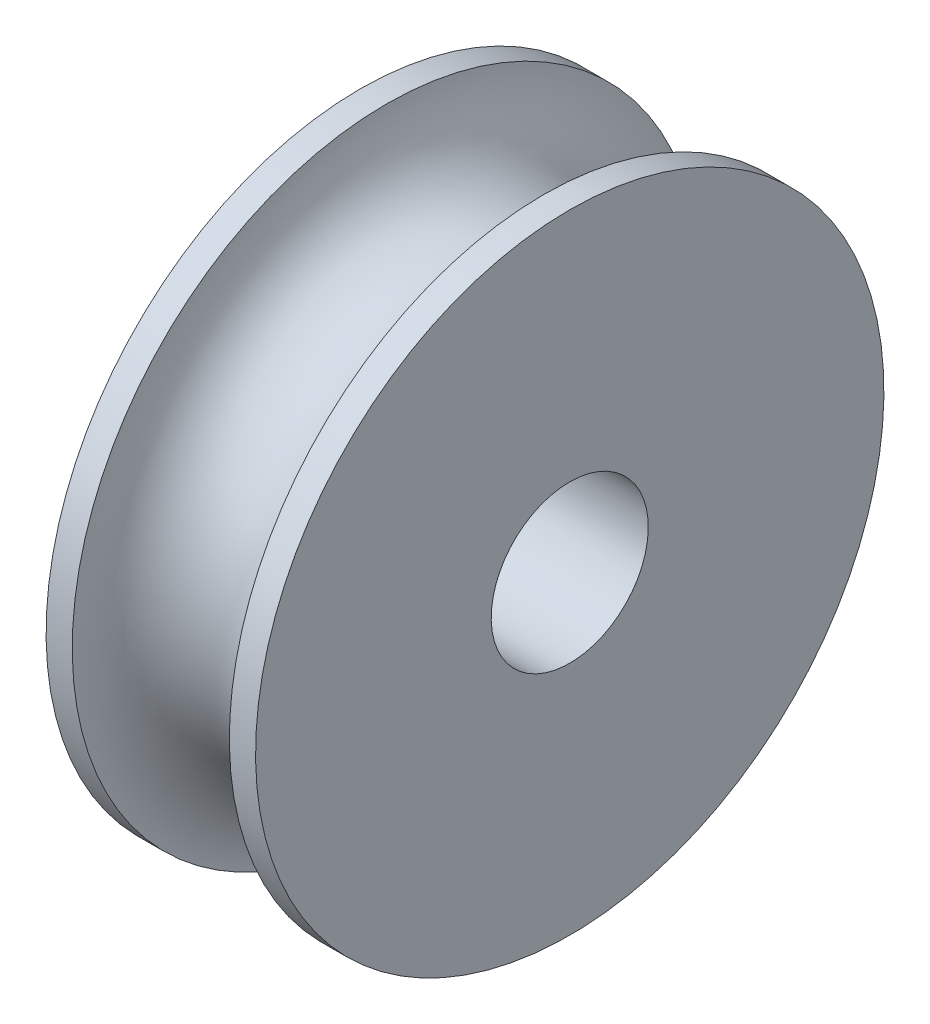
SolidWorks part; units mm, degrees
ref_plane "Ebene vorne" through (0, 0, 0) normal (0, 0, 1) x (1, 0, 0)
ref_plane "Ebene oben" through (0, 0, 0) normal (0, 1, 0) x (1, 0, 0)
ref_plane "Ebene rechts" through (0, 0, 0) normal (1, 0, 0) x (0, 0, -1)
sketch "Skizze1" plane through (0, 0, 0) normal (0, 0, 1) x (1, 0, 0)
  line L0 (0, 0) -> (-4, 0)
  line L1 (-4, 0) -> (-4, 6)
  line L2 (0, 0) -> (0, 6)
  line L3 (-4, 6) -> (-3.5, 6)
  line L4 (0, 6) -> (-0.5, 6)
  arc A1 (-0.5, 6) -> (-3.5, 6) centre (-2, 6) cw
revolve "Rotation1" add sketch "Skizze1" angle 360 about L0
sketch "Skizze2" plane through (0, 0, 0) normal (1, 0, 0) x (0, 0, -1)
  circle A0 centre (0, 0) radius 1.5
extrude "Schnitt-Linear austragen1" cut sketch "Skizze2" against normal blind 10
